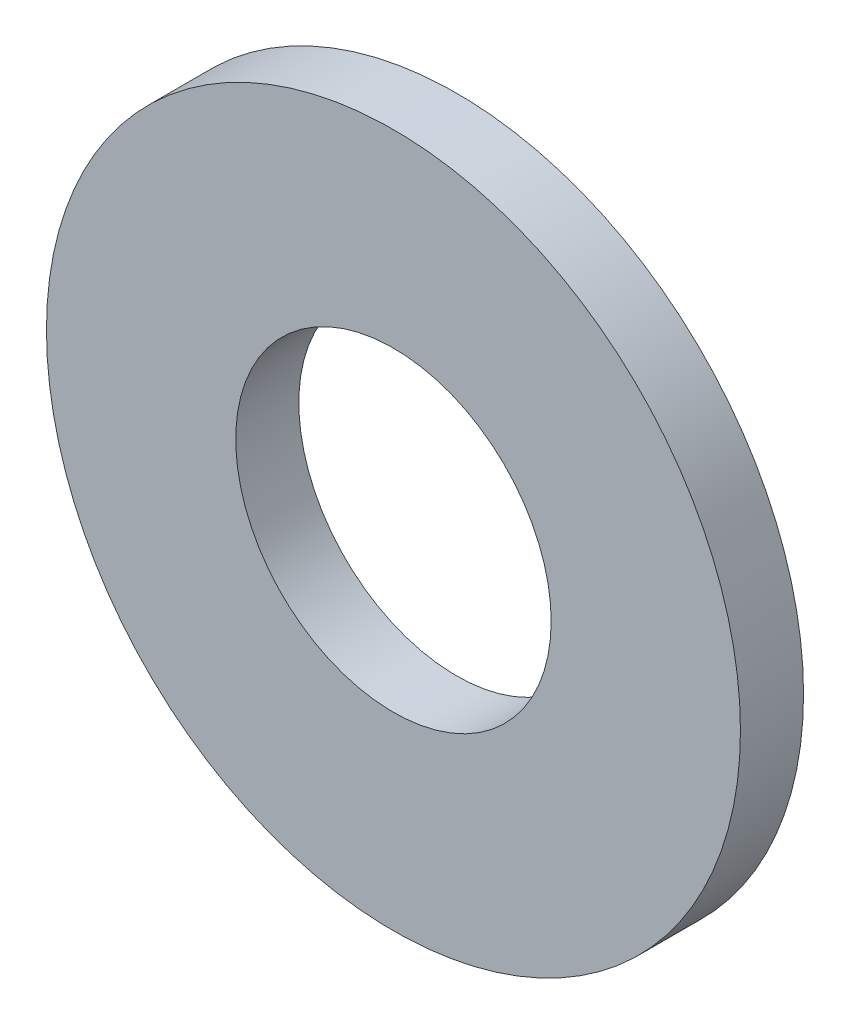
SolidWorks part; units mm, degrees
ref_plane "Front Plane" through (0, 0, 0) normal (0, 0, 1) x (1, 0, 0)
ref_plane "Top Plane" through (0, 0, 0) normal (0, 1, 0) x (1, 0, 0)
ref_plane "Right Plane" through (0, 0, 0) normal (1, 0, 0) x (0, 0, -1)
sketch "Sketch1" plane through (0, 0, 0) normal (0, 0, 1) x (1, 0, 0)
  circle A0 centre (0, 0) radius 11
  circle A1 centre (0, 0) radius 5
  dimension "D1" = 22
  dimension "D2" = 10
extrude "Boss-Extrude1" add sketch "Sketch1" along normal blind 2
